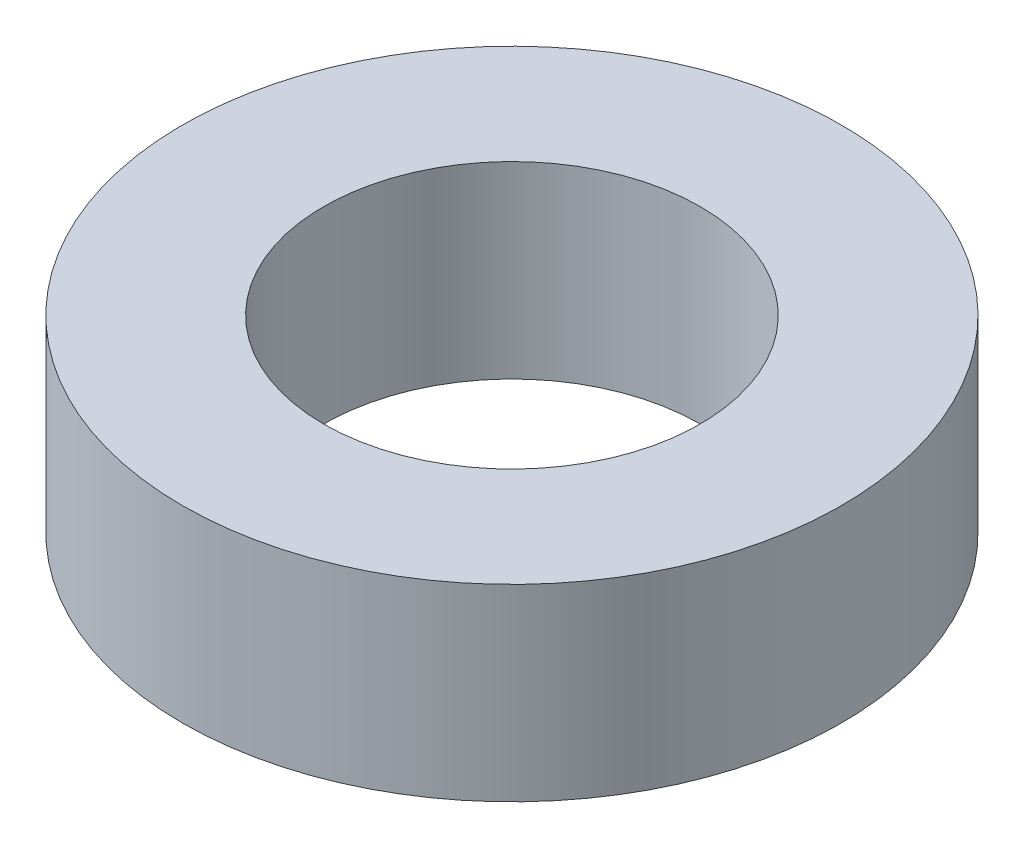
SolidWorks part; units mm, degrees
ref_plane "Front Plane" through (0, 0, 0) normal (0, 0, 1) x (1, 0, 0)
ref_plane "Top Plane" through (0, 0, 0) normal (0, 1, 0) x (1, 0, 0)
ref_plane "Right Plane" through (0, 0, 0) normal (1, 0, 0) x (0, 0, -1)
sketch "Sketch1" plane through (0, 0, 0) normal (0, 1, 0) x (1, 0, 0)
  circle A0 centre (0, 0) radius 7
  circle A1 centre (0, 0) radius 4
  dimension "D1" = 14
  dimension "D2" = 8
extrude "Boss-Extrude1" add sketch "Sketch1" along normal blind 4
